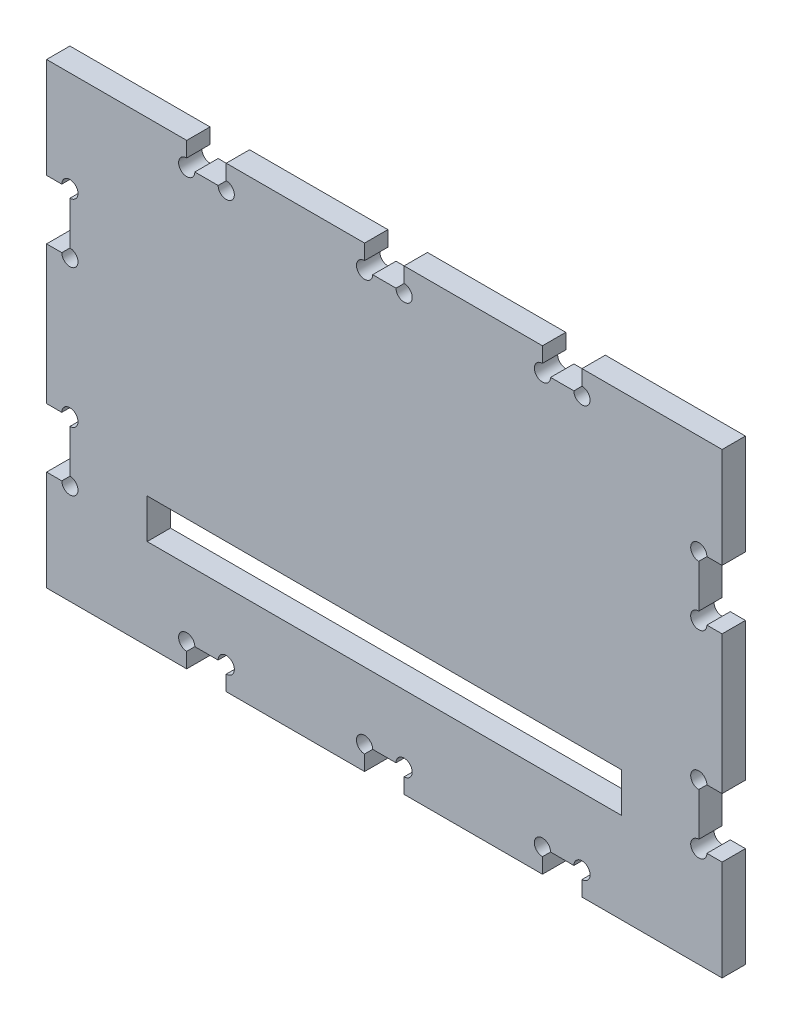
SolidWorks part; units mm, degrees
ref_plane "Front Plane" through (0, 0, 0) normal (0, 0, 1) x (1, 0, 0)
ref_plane "Top Plane" through (0, 0, 0) normal (0, 1, 0) x (1, 0, 0)
ref_plane "Right Plane" through (0, 0, 0) normal (1, 0, 0) x (0, 0, -1)
sketch "Sketch1" plane through (0, 0, 0) normal (0, 0, 1) x (1, 0, 0)
  line L1 (85.45, 57.895) -> (-85.45, 57.895)
  line L2 (85.45, 57.895) -> (85.45, -57.895)
  line L3 (85.45, -57.895) -> (-85.45, -57.895)
  line L4 (-85.45, 57.895) -> (-85.45, -57.895)
  line L5 (85.45, 57.895) -> (-85.45, -57.895) construction
  line L6 (85.45, -57.895) -> (-85.45, 57.895) construction
  point P0 (0, 0)
  dimension "D1" = 170.9
  dimension "D2" = 115.79
extrude "Boss-Extrude1" add sketch "Sketch1" along normal blind 5.9
sketch "Sketch2" plane through (0, 0, 5.9) normal (0, 0, 1) x (1, 0, 0)
  line L0 (-85.45, 57.895) -> (-85.45, -57.895) construction
  line L1 (-85.45, 32.5) -> (-79.55, 32.5)
  line L2 (-85.45, 32.5) -> (-85.45, 17.5)
  line L3 (-85.45, 17.5) -> (-79.55, 17.5)
  line L4 (-79.55, 32.5) -> (-79.55, 17.5)
  line L6 (-85.45, -17.5) -> (-79.55, -17.5)
  line L7 (-85.45, -17.5) -> (-85.45, -32.5)
  line L8 (-85.45, -32.5) -> (-79.55, -32.5)
  line L9 (-79.55, -17.5) -> (-79.55, -32.5)
  line L10 (-85.45, 17.5) -> (-85.45, -17.5) construction
  line L11 (0, 0) -> (0, 57.895) construction
  line L12 (85.45, 57.895) -> (-85.45, 57.895) construction
  line L13 (85.45, 17.5) -> (85.45, -17.5) construction
  line L14 (79.55, -17.5) -> (79.55, -32.5)
  line L15 (85.45, -32.5) -> (79.55, -32.5)
  line L16 (85.45, -17.5) -> (85.45, -32.5)
  line L17 (85.45, -17.5) -> (79.55, -17.5)
  line L18 (79.55, 32.5) -> (79.55, 17.5)
  line L19 (85.45, 17.5) -> (79.55, 17.5)
  line L20 (85.45, 32.5) -> (85.45, 17.5)
  line L21 (85.45, 32.5) -> (79.55, 32.5)
  line L22 (-40, 57.895) -> (40, 57.895) construction
  line L23 (-50, 57.895) -> (-40, 57.895)
  line L24 (-50, 57.895) -> (-50, 51.995)
  line L25 (-50, 51.995) -> (-40, 51.995)
  line L26 (-40, 57.895) -> (-40, 51.995)
  line L27 (-5, 57.895) -> (5, 57.895)
  line L28 (-5, 57.895) -> (-5, 51.995)
  line L29 (-5, 51.995) -> (5, 51.995)
  line L30 (5, 57.895) -> (5, 51.995)
  line L31 (40, 57.895) -> (50, 57.895)
  line L32 (40, 57.895) -> (40, 51.995)
  line L33 (40, 51.995) -> (50, 51.995)
  line L34 (50, 57.895) -> (50, 51.995)
  line L35 (0, 0) -> (35.7923, 0) construction
  line L36 (-40, -57.895) -> (40, -57.895) construction
  line L37 (50, -57.895) -> (50, -51.995)
  line L38 (40, -51.995) -> (50, -51.995)
  line L39 (40, -57.895) -> (40, -51.995)
  line L40 (40, -57.895) -> (50, -57.895)
  line L41 (5, -57.895) -> (5, -51.995)
  line L42 (-5, -51.995) -> (5, -51.995)
  line L43 (-5, -57.895) -> (-5, -51.995)
  line L44 (-5, -57.895) -> (5, -57.895)
  line L45 (-40, -57.895) -> (-40, -51.995)
  line L46 (-50, -51.995) -> (-40, -51.995)
  line L47 (-50, -57.895) -> (-50, -51.995)
  line L48 (-50, -57.895) -> (-40, -57.895)
  point P10 (-85.45, 0)
  point P36 (40, 54.945)
  point P37 (0, 57.895)
  dimension "D1" = 15
  dimension "D2" = 35
  dimension "D4" = 10
  dimension "D5" = 5.9
  dimension "D6" = 35
  dimension "D7" = 35
extrude "Cut-Extrude1" cut sketch "Sketch2" against normal through all
sketch "Sketch4" plane through (0, 0, 5.9) normal (0, 0, 1) x (1, 0, 0)
  line L1 (-60, -35) -> (60, -35)
  line L2 (-60, -35) -> (-60, -25)
  line L3 (-60, -25) -> (60, -25)
  line L4 (60, -35) -> (60, -25)
  line L5 (-60, -35) -> (60, -25) construction
  line L6 (-60, -25) -> (60, -35) construction
  point P4 (0, -30)
  dimension "D1" = 25
  dimension "D2" = 10
  dimension "D3" = 120
extrude "Cut-Extrude2" cut sketch "Sketch4" against normal up to next
sketch "Sketch5" plane through (0, 0, 5.9) normal (0, 0, 1) x (1, 0, 0)
  circle A0 centre (-50, 51.995) radius 2.05
  circle A1 centre (-40, 51.995) radius 2.05
  circle A2 centre (-5, 51.995) radius 2.05
  circle A3 centre (5, 51.995) radius 2.05
  circle A4 centre (40, 51.995) radius 2.05
  circle A5 centre (50, 51.995) radius 2.05
  circle A6 centre (79.55, 32.5) radius 2.05
  circle A7 centre (79.55, 17.5) radius 2.05
  circle A8 centre (79.55, -17.5) radius 2.05
  circle A9 centre (79.55, -32.5) radius 2.05
  circle A10 centre (-40, -51.995) radius 2.05
  circle A11 centre (-5, -51.995) radius 2.05
  circle A12 centre (5, -51.995) radius 2.05
  circle A13 centre (40, -51.995) radius 2.05
  circle A14 centre (50, -51.995) radius 2.05
  circle A15 centre (-50, -51.995) radius 2.05
  circle A16 centre (-79.55, -32.5) radius 2.05
  circle A17 centre (-79.55, -17.5) radius 2.05
  circle A18 centre (-79.55, 17.5) radius 2.05
  circle A19 centre (-79.55, 32.5) radius 2.05
  dimension "D1" = 4.1
extrude "Cut-Extrude3" cut sketch "Sketch5" against normal up to next
equation "\"e\" = 5.9"
equation "\"D1@Boss-Extrude1\"=\"e\""
equation "\"D1@Sketch1\"= 165 + \"e\""
equation "\"D5@Sketch2\"= \"e\""
equation "\"D2@Sketch1\"= 109.89 + \"e\""
